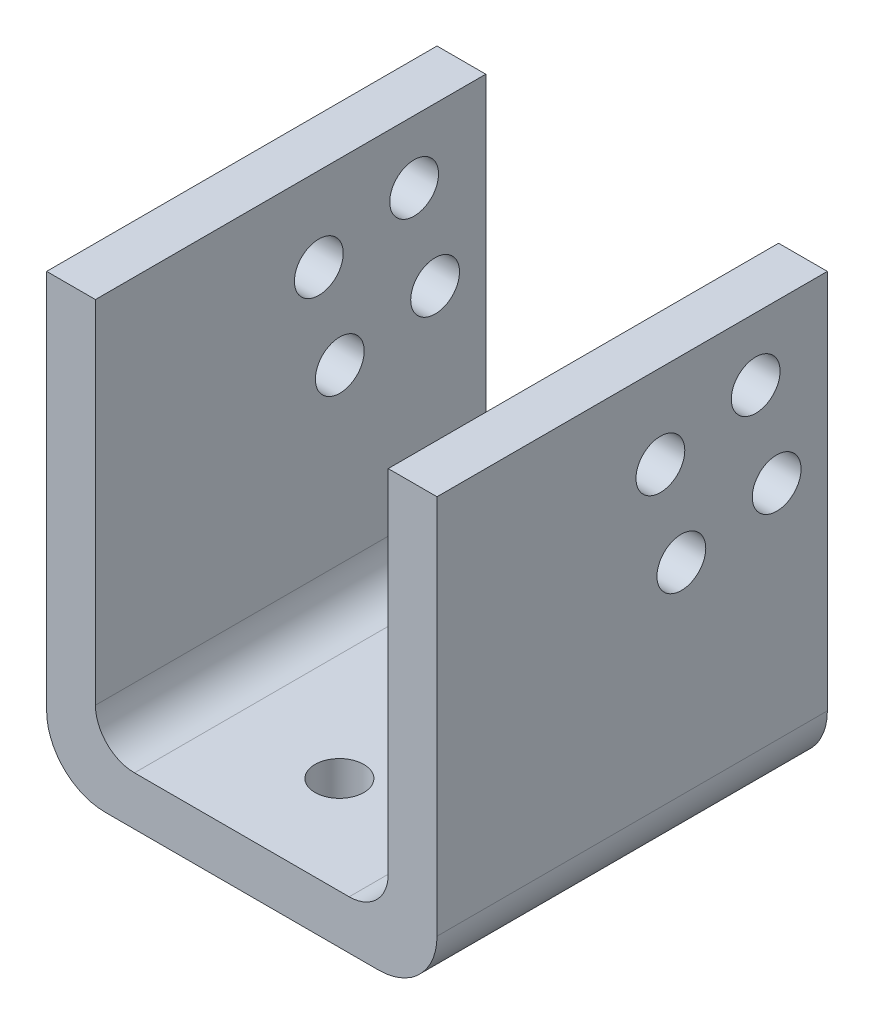
SolidWorks part; units mm, degrees
material "ABS"
ref_plane "Plano frontal" through (0, 0, 0) normal (0, 0, 1) x (1, 0, 0)
ref_plane "Plano superior" through (0, 0, 0) normal (0, 1, 0) x (1, 0, 0)
ref_plane "Plano direito" through (0, 0, 0) normal (1, 0, 0) x (0, 0, -1)
sketch "Esboço1" plane through (0, 0, 0) normal (0, 0, 1) x (1, 0, 0)
  line L0 (0, 0) -> (0, 45)
  line L1 (0, 45) -> (5, 45)
  line L2 (5, 45) -> (5, 5)
  line L3 (5, 5) -> (35, 5)
  line L4 (35, 5) -> (35, 45)
  line L5 (35, 45) -> (40, 45)
  line L6 (40, 45) -> (40, 0)
  line L7 (40, 0) -> (0, 0)
  dimension "D1" = 5
  dimension "D2" = 30
  dimension "D3" = 45
  dimension "D4" = 40
extrude "Ressalto-extrusão1" add sketch "Esboço1" along normal blind 40
fillet "Filete1" radius 6 2 edges at (40, 0, 20) (0, 0, 20)
sketch "Esboço3" plane through (0, 0, 0) normal (-1, 0, 0) x (0, 0, 1)
  circle A0 centre (7.3429, 38.577) radius 2.5
  circle A1 centre (17.1092, 36.428) radius 2.5
  circle A2 centre (14.9603, 26.6617) radius 2.5
  circle A3 centre (5.1939, 28.8106) radius 2.5
extrude "Corte-extrusão1" cut sketch "Esboço3" against normal blind 60
fillet "Filete2" radius 4 2 edges at (5, 5, 20) (35, 5, 20)
sketch "Esboço6" plane through (0, 0, 0) normal (0, -1, 0) x (1, 0, 0)
  line L0 (6, 20) -> (34, 20) construction
  line L4 (6, 0) -> (34, 0)
  line L5 (34, 0) -> (34, 40)
  line L6 (34, 40) -> (6, 40)
  line L7 (6, 40) -> (6, 0)
  line L9 (34, 0) -> (34, 40)
  line L11 (6, 40) -> (6, 0)
  circle A0 centre (20, 30) radius 2.5
  circle A1 centre (20, 10) radius 2.5
  point P10 (0, 0)
  point P12 (18.9935, 40)
  dimension "D2" = 5
  dimension "D3" = 10
  dimension "D4" = 14
  dimension "D1" = 0
extrude "Corte-extrusão4" cut sketch "Esboço6" against normal blind 5 contours A0 | A1
